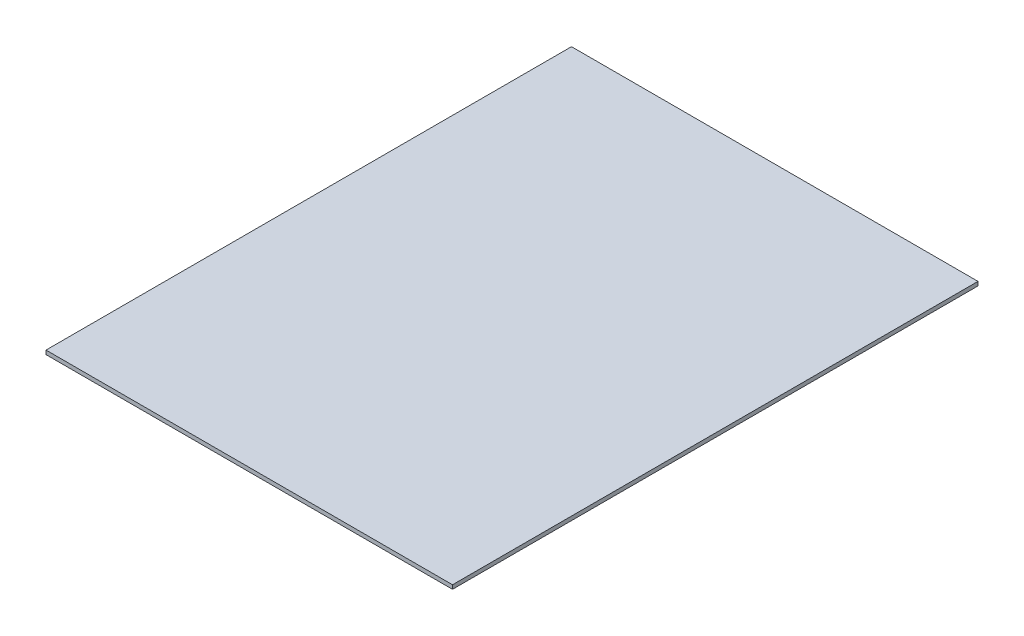
SolidWorks part; units mm, degrees
ref_plane "Front Plane" through (0, 0, 0) normal (0, 0, 1) x (1, 0, 0)
ref_plane "Top Plane" through (0, 0, 0) normal (0, 1, 0) x (1, 0, 0)
ref_plane "Right Plane" through (0, 0, 0) normal (1, 0, 0) x (0, 0, -1)
sketch "Sketch1" plane through (0, 0, 0) normal (0, 1, 0) x (1, 0, 0)
  line L1 (0, 0) -> (520.7, 0)
  line L2 (0, 0) -> (0, -673.1)
  line L3 (0, -673.1) -> (520.7, -673.1)
  line L4 (520.7, 0) -> (520.7, -673.1)
extrude "Boss-Extrude1" add sketch "Sketch1" along normal blind 5.08
